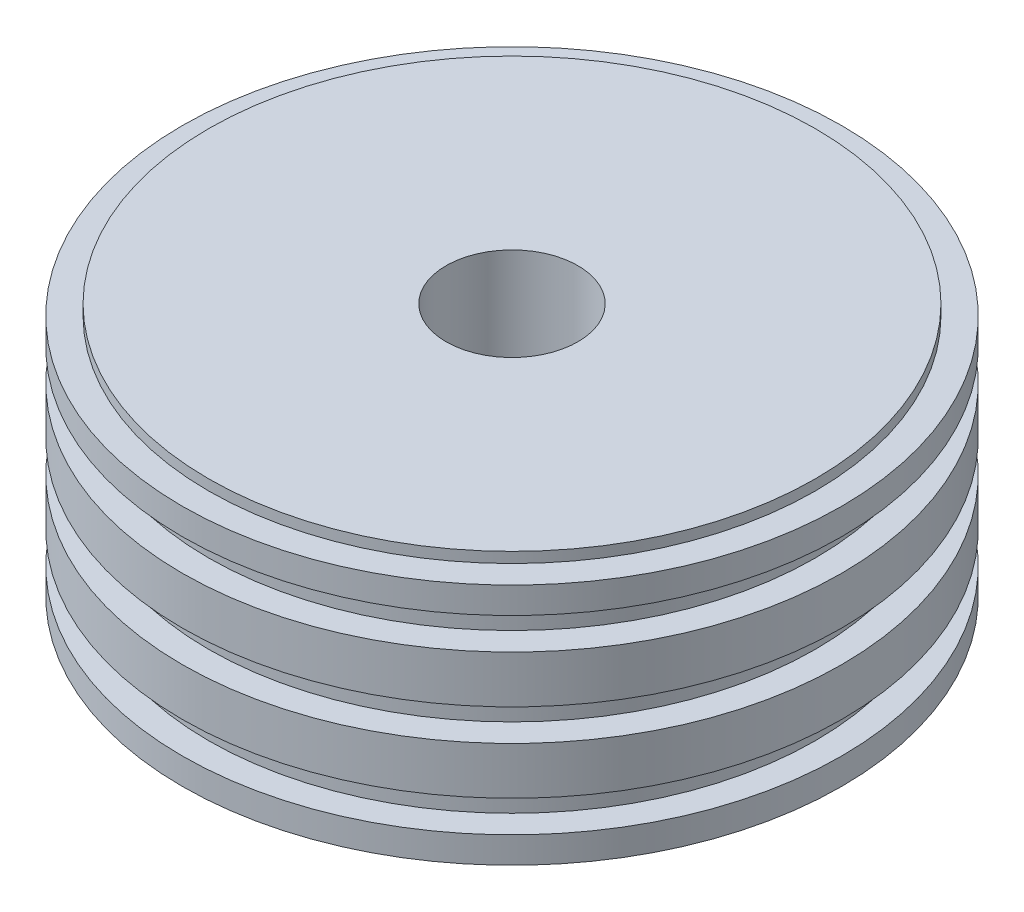
SolidWorks part; units mm, degrees
ref_plane "前视基准面" through (0, 0, 0) normal (0, 0, 1) x (1, 0, 0)
ref_plane "上视基准面" through (0, 0, 0) normal (0, 1, 0) x (1, 0, 0)
ref_plane "右视基准面" through (0, 0, 0) normal (1, 0, 0) x (0, 0, -1)
other "Configuration Table"
sketch "草图1" plane through (0, 0, 0) normal (0, 1, 0) x (1, 0, 0)
  circle A0 centre (0, 0) radius 62.5
  dimension "D1" = 125
extrude "凸台-拉伸1" add sketch "草图1" along normal blind 50
sketch "草图2" plane through (0, 50, 0) normal (0, 1, 0) x (1, 0, 0)
  circle A0 centre (0, 0) radius 57.5
  circle A1 centre (0, 0) radius 62.5 construction
  circle A2 centre (0, 0) radius 62.5
  dimension "D1" = 115
extrude "切除-拉伸1" cut sketch "草图2" against normal blind 6 from offset 7 offset against normal yes
pattern_linear "阵列(线性)1" count 3 spacing 15 along (0, -1, 0) of "切除-拉伸1"
sketch "草图3" plane through (0, 50, 0) normal (0, 1, 0) x (1, 0, 0)
  circle A0 centre (0, 0) radius 62.5 construction
  circle A1 centre (0, 0) radius 62.5
  circle A2 centre (0, 0) radius 57.5
  dimension "D1" = 115
extrude "切除-拉伸2" cut sketch "草图3" against normal blind 2
sketch "草图4" plane through (0, 0, 0) normal (0, -1, 0) x (1, 0, 0)
  circle A0 centre (0, 0) radius 62.5 construction
  circle A1 centre (0, 0) radius 62.5
  circle A2 centre (0, 0) radius 57.5
  dimension "D1" = 115
extrude "切除-拉伸3" cut sketch "草图4" against normal blind 2
sketch "草图5" plane through (0, 50, 0) normal (0, 1, 0) x (1, 0, 0)
  circle A0 centre (0, 0) radius 12.5
extrude "切除-拉伸4" cut sketch "草图5" against normal through all
